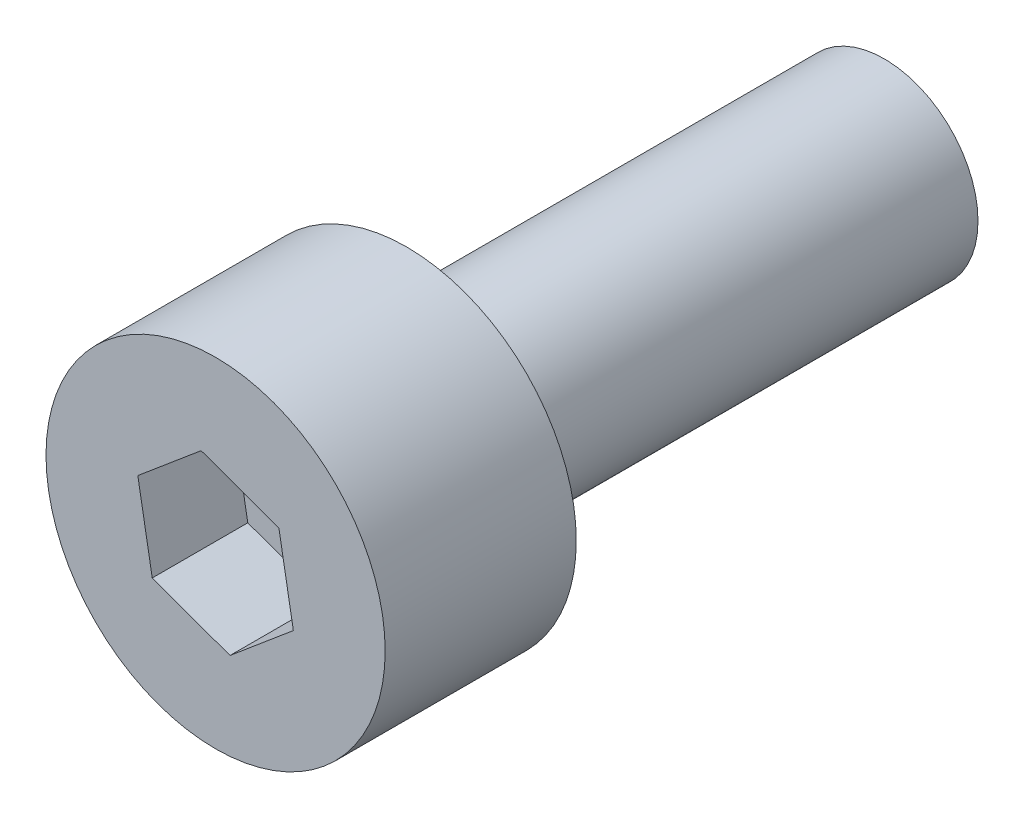
SolidWorks part; units mm, degrees
ref_plane "Front" through (0, 0, 0) normal (0, 0, 1) x (1, 0, 0)
ref_plane "Top" through (0, 0, 0) normal (0, 1, 0) x (1, 0, 0)
ref_plane "Right" through (0, 0, 0) normal (1, 0, 0) x (0, 0, -1)
sketch "Sketch1" plane through (0, 0, 0) normal (0, 0, 1) x (1, 0, 0)
  circle A0 centre (0, 0) radius 1.96
  dimension "D1" = 3.92
extrude "Boss-Extrude1" add sketch "Sketch1" along normal blind 10
sketch "Sketch2" plane through (0, 0, 10) normal (0, 0, 1) x (1, 0, 0)
  circle A0 centre (0, 0) radius 3.55
  dimension "D1" = 7.1
extrude "Boss-Extrude2" add sketch "Sketch2" along normal blind 4
sketch "Sketch3" plane through (0, 0, 14) normal (0, 0, 1) x (1, 0, 0)
  line L1 (1.3258, 1.1145) -> (-0.3023, 1.7055)
  line L2 (-0.3023, 1.7055) -> (-1.6281, 0.5909)
  line L3 (-1.6281, 0.5909) -> (-1.3258, -1.1145)
  line L4 (-1.3258, -1.1145) -> (0.3023, -1.7055)
  line L5 (0.3023, -1.7055) -> (1.6281, -0.5909)
  line L6 (1.6281, -0.5909) -> (1.3258, 1.1145)
  circle A0 centre (0, 0) radius 1.5 construction
  dimension "D1" = 3
extrude "Cut-Extrude1" cut sketch "Sketch3" against normal blind 2
